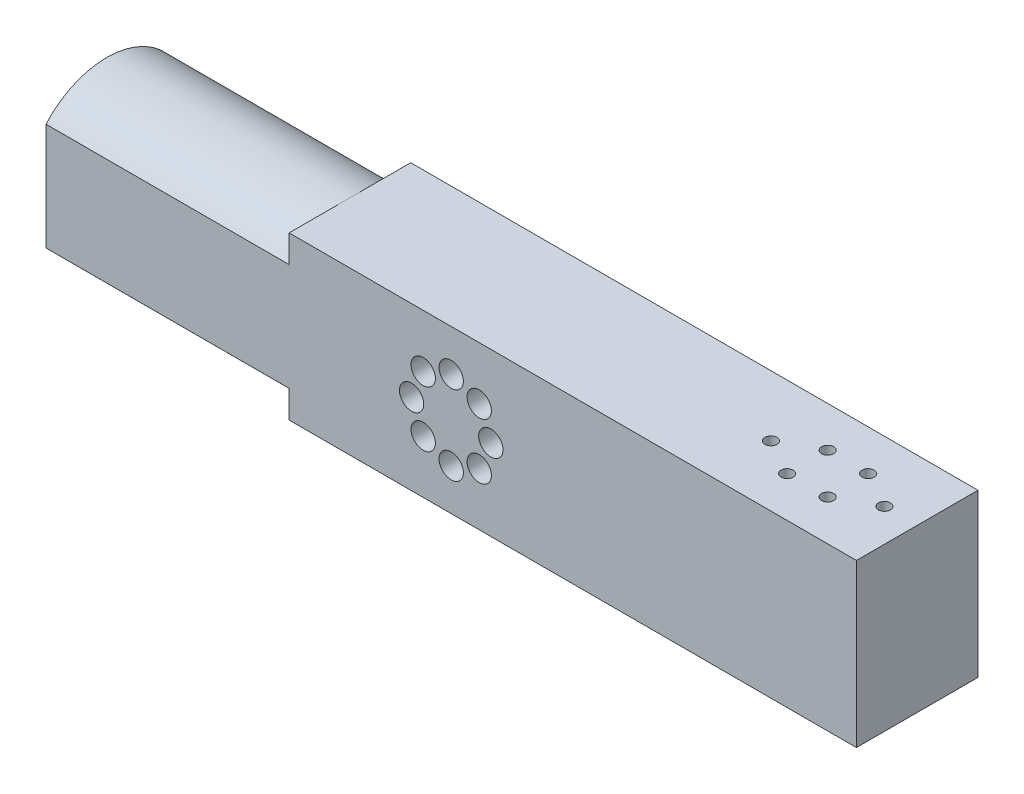
SolidWorks part; units mm, degrees
ref_plane "Alzado" through (0, 0, 0) normal (0, 0, 1) x (1, 0, 0)
ref_plane "Planta" through (0, 0, 0) normal (0, 1, 0) x (1, 0, 0)
ref_plane "Vista lateral" through (0, 0, 0) normal (1, 0, 0) x (0, 0, -1)
sketch "Croquis1" plane through (0, 0, 0) normal (0, 0, 1) x (1, 0, 0)
  line L0 (0, 0) -> (0, 9.779) construction
  line L2 (-100, -20) -> (100, -20)
  line L3 (-100, -20) -> (-100, 20)
  line L4 (-100, 20) -> (100, 20)
  line L5 (100, -20) -> (100, 20)
  line L6 (-100, -20) -> (100, 20) construction
  line L7 (-100, 20) -> (100, -20) construction
  circle A1 centre (0, 9.779) radius 2
  circle A2 centre (6.9148, 6.9148) radius 2
  circle A3 centre (9.779, 0) radius 2
  circle A4 centre (6.9148, -6.9148) radius 2
  circle A5 centre (0, -9.779) radius 2
  circle A6 centre (-6.9148, -6.9148) radius 2
  circle A7 centre (-9.779, 0) radius 2
  circle A8 centre (-6.9148, 6.9148) radius 2
  point P22 (0, 0)
  dimension "D1" = 8
extrude "Saliente-Extruir1" add sketch "Croquis1" along normal blind 10
sketch "Croquis2" plane through (0, 0, 10) normal (0, 0, 1) x (1, 0, 0)
  line L1 (100, 20) -> (-100, 20)
  line L2 (100, 20) -> (100, -20)
  line L3 (100, -20) -> (-100, -20)
  line L4 (-100, 20) -> (-100, -20)
  line L5 (100, 20) -> (-100, -20) construction
  line L6 (100, -20) -> (-100, 20) construction
  line L7 (-100, 13) -> (100, 13)
  line L8 (-100, 13) -> (-100, -13)
  line L9 (-100, -13) -> (100, -13)
  line L10 (100, 13) -> (100, -13)
  line L11 (-100, 13) -> (100, -13) construction
  line L12 (-100, -13) -> (100, 13) construction
  point P0 (0, 0)
  point P7 (0, 0)
  line M9 (100, -20) -> (100, 20)
  line M10 (100, 20) -> (-100, 20)
  line M11 (-100, 20) -> (-100, -20)
  line M12 (-100, -20) -> (100, -20)
extrude "Saliente-Extruir3" add sketch "Croquis2" along normal blind 20 contours L9 M11 M12 M9 | L7 L2 M11 M10
sketch "Croquis3" plane through (0, 0, 10) normal (0, 0, 1) x (1, 0, 0)
  line L0 (-100, -13) -> (100, -13) construction
  line L1 (-16, 13) -> (16, 13)
  line L2 (-16, 13) -> (-16, -13)
  line L3 (-16, -13) -> (16, -13)
  line L4 (16, 13) -> (16, -13)
  line L5 (-16, 13) -> (16, -13) construction
  line L6 (-16, -13) -> (16, 13) construction
  line L8 (-100, -13) -> (-16, -13)
  line L9 (-100, -13) -> (-100, 13)
  line L10 (-100, 13) -> (-16, 13)
  line L11 (-16, -13) -> (-16, 13)
  line L12 (16, -13) -> (100, -13)
  line L13 (16, -13) -> (16, 13)
  line L14 (16, 13) -> (100, 13)
  line L15 (100, -13) -> (100, 13)
  point P0 (0, 0)
  line M21 (100, 13) -> (-100, 13)
  line M22 (-100, 13) -> (-100, -13)
  line M23 (-100, -13) -> (100, -13)
  line M24 (100, -13) -> (100, 13)
extrude "Saliente-Extruir4" add sketch "Croquis3" along normal blind 20 contours L2 M21 M22 M23 | L4 M21 M23 M24
sketch "Croquis5" plane through (0, 20, 0) normal (0, -1, 0) x (-1, 0, 0)
  line L13 (-55.8, -5) -> (-100, -25) construction
  line L14 (-100, -5) -> (-55.8, -25) construction
  circle A0 centre (-63.9, -15) radius 1.5
  circle A1 centre (-72.9, -10) radius 1.5
  circle A2 centre (-72.9, -20) radius 1.5
  circle A3 centre (-82.9, -20) radius 1.5
  circle A4 centre (-82.9, -10) radius 1.5
  circle A5 centre (-91.9, -15) radius 1.5
extrude "Cortar-Extruir1" cut sketch "Croquis5" along normal blind 10
sketch "Croquis6" plane through (-100, 0, 0) normal (-1, 0, 0) x (0, 0, 1)
  line L2 (-8.9319, -20) -> (38.9319, -20)
  line L3 (-8.9319, -20) -> (-8.9319, 20)
  line L4 (-8.9319, 20) -> (38.9319, 20)
  line L5 (38.9319, -20) -> (38.9319, 20)
  line L6 (-8.9319, -20) -> (38.9319, 20) construction
  line L7 (-8.9319, 20) -> (38.9319, -20) construction
  circle A1 centre (15, 0) radius 20
  line M7 (0, 20) -> (0, -20)
  line M8 (0, -20) -> (30, -20)
  line M9 (30, -20) -> (30, 20)
  line M10 (30, 20) -> (0, 20)
extrude "Cortar-Extruir2" cut sketch "Croquis6" against normal blind 60 contours A1 L4 L3 L2 M7 | A1 L2 L5 L4 M9 | A1 L2 M9 | A1 M7 M8 | A1 L4 M7 | A1 M9 M10
sketch "Croquis7" plane through (0, 0, 10) normal (0, 0, 1) x (1, 0, 0)
  circle A0 centre (0, 9.779) radius 3
  circle A1 centre (-6.9148, 6.9148) radius 3
  circle A2 centre (-9.779, 0) radius 3
  circle A3 centre (6.9148, 6.9148) radius 3
  circle A4 centre (9.779, 0) radius 3
  circle A5 centre (-6.9148, -6.9148) radius 3
  circle A6 centre (6.9148, -6.9148) radius 3
  circle A7 centre (0, -9.779) radius 3
sketch "Croquis8" plane through (0, 0, 10) normal (0, 0, 1) x (1, 0, 0)
  line L1 (-16, 13) -> (16, 13)
  line L2 (-16, 13) -> (-16, -13)
  line L3 (-16, -13) -> (16, -13)
  line L4 (16, 13) -> (16, -13)
extrude "Saliente-Extruir5" add sketch "Croquis8" along normal up to vertex (20 mm away)
extrude "Cortar-Extruir3" cut sketch "Croquis7" along normal up to vertex (20 mm away)
